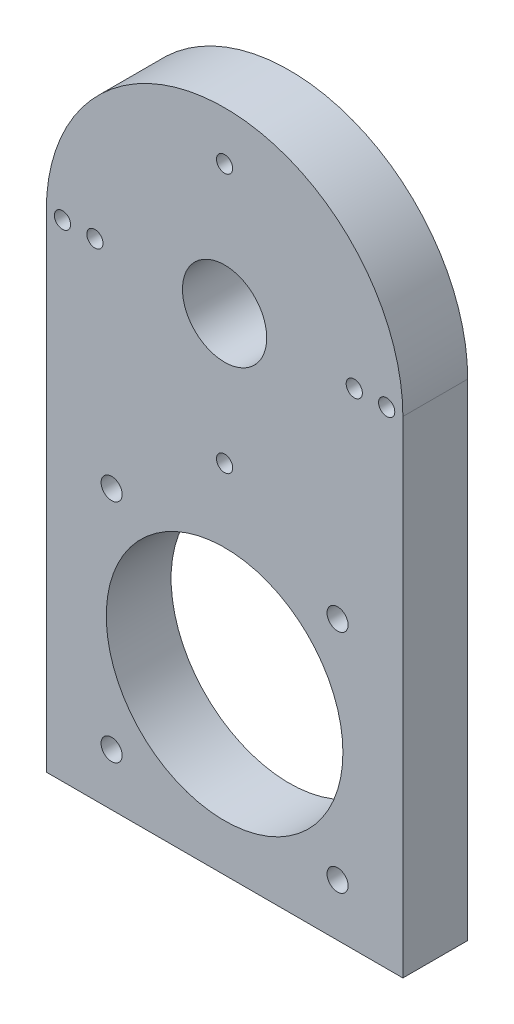
SolidWorks part; units mm, degrees
ref_plane "Front Plane" through (0, 0, 0) normal (0, 0, 1) x (1, 0, 0)
ref_plane "Top Plane" through (0, 0, 0) normal (0, 1, 0) x (1, 0, 0)
ref_plane "Right Plane" through (0, 0, 0) normal (1, 0, 0) x (0, 0, -1)
sketch "Sketch1" plane through (0, 0, 0) normal (0, 0, 1) x (1, 0, 0)
  line L0 (-57.2515, 0) -> (52.7485, 0)
  line L1 (52.7485, 0) -> (52.7485, 150)
  line L2 (-57.2515, 0) -> (-57.2515, 150)
  arc A0 (-57.2515, 150) -> (52.7485, 150) centre (-2.2515, 150) cw
  circle A2 centre (-2.2515, 150) radius 13
  dimension "D4" = 26
  dimension "D1" = 110
  dimension "D2" = 150
  dimension "D3" = 150
extrude "Boss-Extrude1" add sketch "Sketch1" along normal blind 20
sketch "Sketch3" plane through (0, 0, 20) normal (0, 0, 1) x (1, 0, 0)
  circle A0 centre (-2.2515, 150) radius 40 construction
  point P3 (-2.2515, 190)
  point P4 (37.7485, 150)
  point P5 (-2.2515, 110)
  point P6 (-42.2515, 150)
  dimension "D1" = 80
hole_wizard "Ø5.0mm Dowel Hole1" positions "3DSketch1" profile "Sketch4" hole size "Ø5.0" standard "ANSI Metric" end condition through all
sketch3d "3DSketch1"
  point P0 (-2.2515, 190, 20)
  point P3 (37.7485, 150, 20)
  point P6 (-2.2515, 110, 20)
  point P9 (-42.2515, 150, 20)
sketch "Sketch4" plane through (-2.2515, 190, 20) normal (1, 0, 0) x (0, -1, 0)
  line L0 (0, 0) -> (0, 20)
  line L1 (0, 20) -> (2.5, 20)
  line L2 (2.5, 20) -> (2.5, 0)
  line L5 (2.5, 0) -> (0, 0)
  line L11 (0, -6.35) -> (0, 107.95) construction
  dimension "Thru Hole Dia." = 5
  dimension "Thru Hole Depth" = 20
sketch "Sketch5" plane through (0, 0, 0) normal (0, -1, 0) x (-1, 0, 0)
  line L0 (57.2515, -20) -> (57.2515, 0) construction
  line L1 (-52.7485, -20) -> (-52.7485, 0) construction
  line L2 (57.2515, 0) -> (-52.7485, 0) construction
  point P0 (42.2515, -10)
  point P1 (-37.7485, -10)
  dimension "D1" = 15
  dimension "D2" = 15
  dimension "D3" = 10
hole_wizard "Ø5.0mm Dowel Hole2" positions "3DSketch2" profile "Sketch6" hole size "Ø5.0" standard "ANSI Metric"
sketch3d "3DSketch2"
  point P0 (-42.2515, 0, 10)
  point P3 (37.7485, 0, 10)
sketch "Sketch6" plane through (-42.2515, 0, 10) normal (1, 0, 0) x (0, 0, -1)
  line L0 (0, 0) -> (0, 147.5)
  line L1 (0, 147.5) -> (2.5, 147.5)
  line L2 (2.5, 147.5) -> (2.5, 0)
  line L5 (2.5, 0) -> (0, 0)
  line L11 (0, -6.35) -> (0, 107.95) construction
  dimension "Thru Hole Dia." = 5
  dimension "Thru Hole Depth" = 147.5
sketch "Sketch7" plane through (0, 0, 20) normal (0, 0, 1) x (1, 0, 0)
  point P0 (-52.2515, 150)
  point P1 (47.7485, 150)
  dimension "D1" = 10
  dimension "D2" = 10
hole_wizard "Ø5.0mm Dowel Hole3" positions "3DSketch3" profile "Sketch8" hole size "Ø5.0" standard "ANSI Metric" end condition up to next
sketch3d "3DSketch3"
  point P0 (-52.2515, 150, 20)
  point P3 (47.7485, 150, 20)
sketch "Sketch8" plane through (-52.2515, 150, 20) normal (1, 0, 0) x (0, -1, 0)
  line L0 (0, 0) -> (0, 20)
  line L1 (0, 20) -> (2.5, 20)
  line L2 (2.5, 20) -> (2.5, 0)
  line L5 (2.5, 0) -> (0, 0)
  line L11 (0, -6.35) -> (0, 107.95) construction
  dimension "Thru Hole Dia." = 5
  dimension "Thru Hole Depth" = 20
sketch "Sketch9" plane through (0, 0, 20) normal (0, 0, 1) x (1, 0, 0)
  circle A0 centre (-2.2515, 51) radius 36.5
  dimension "D1" = 73
extrude "Cut-Extrude1" cut sketch "Sketch9" against normal through all
sketch "Sketch10" plane through (0, 0, 20) normal (0, 0, 1) x (1, 0, 0)
  line L1 (32.5985, 85.85) -> (-37.1015, 85.85)
  line L2 (32.5985, 85.85) -> (32.5985, 16.15)
  line L3 (32.5985, 16.15) -> (-37.1015, 16.15)
  line L4 (-37.1015, 85.85) -> (-37.1015, 16.15)
  line L5 (32.5985, 85.85) -> (-37.1015, 16.15) construction
  line L6 (32.5985, 16.15) -> (-37.1015, 85.85) construction
  point P0 (-2.2515, 51)
  dimension "D1" = 69.7
  dimension "D2" = 69.7
hole_wizard "Ø6.0mm Dowel Hole1" positions "3DSketch4" profile "Sketch11" hole size "Ø6.0" standard "ANSI Metric" end condition through all
sketch3d "3DSketch4"
  point P0 (-37.1015, 85.85, 20)
  point P3 (32.5985, 85.85, 20)
  point P6 (32.5985, 16.15, 20)
  point P9 (-37.1015, 16.15, 20)
sketch "Sketch11" plane through (-37.1015, 85.85, 20) normal (1, 0, 0) x (0, -1, 0)
  line L0 (0, 0) -> (0, 20)
  line L1 (0, 20) -> (3.25, 20)
  line L2 (3.25, 20) -> (3.25, 0)
  line L5 (3.25, 0) -> (0, 0)
  line L11 (0, -6.35) -> (0, 107.95) construction
  dimension "Thru Hole Dia." = 6.5
  dimension "Thru Hole Depth" = 20
